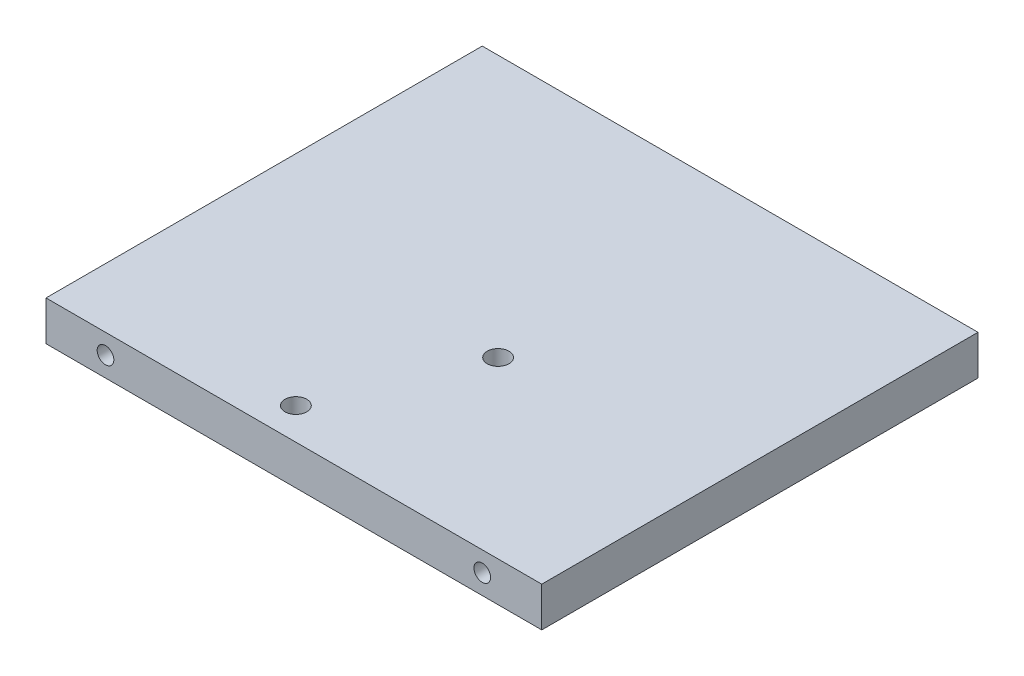
SolidWorks part; units mm, degrees
ref_plane "Front Plane" through (0, 0, 0) normal (0, 0, 1) x (1, 0, 0)
ref_plane "Top Plane" through (0, 0, 0) normal (0, 1, 0) x (1, 0, 0)
ref_plane "Right Plane" through (0, 0, 0) normal (1, 0, 0) x (0, 0, -1)
sketch "Sketch1" plane through (0, 0, 0) normal (0, 1, 0) x (1, 0, 0)
  line L1 (-62.5, -55) -> (62.5, -55)
  line L2 (-62.5, -55) -> (-62.5, 55)
  line L3 (-62.5, 55) -> (62.5, 55)
  line L4 (62.5, -55) -> (62.5, 55)
  line L5 (-62.5, -55) -> (62.5, 55) construction
  line L6 (-62.5, 55) -> (62.5, -55) construction
  circle A0 centre (7.5, -11) radius 2.75
  circle A1 centre (-7.5, -47) radius 2.75
  point P0 (0, 0)
  point P10 (0, 0)
  point P11 (0, 0)
  point P12 (0, 0)
  dimension "D3" = 5.5
  dimension "D4" = 5.5
  dimension "D1" = 125
  dimension "D2" = 110
  dimension "D5" = 8
  dimension "D6" = 11
  dimension "D7" = 7.5
  dimension "D8" = 7.5
extrude "Boss-Extrude1" add sketch "Sketch1" along normal blind 10
hole_wizard "M5 Tapped Hole3" positions "Sketch9" profile "Sketch10" tap size "M5" standard "DIN"
sketch "Sketch9" plane through (0, 0, -55) normal (0, 0, -1) x (-1, 0, 0)
  line L0 (-62.5, 10) -> (-62.5, 0) construction
  point P0 (-47.5, 5)
  point P2 (47.5, 5)
  point P7 (0, 0)
  point P8 (0, 0)
  dimension "D1" = 15
  dimension "D2" = 95
sketch "Sketch10" plane through (47.5, 5, -55) normal (1, 0, 0) x (0, 1, 0)
  line L0 (0, 0) -> (0, 17.2618)
  line L1 (0, 17.2618) -> (2.1, 16)
  line L2 (2.1, 16) -> (2.1, 0)
  line L5 (2.1, 0) -> (0, 0)
  line L10 (0, 17.2618) -> (-2.1, 16) construction
  line L11 (0, -6.35) -> (0, 107.95) construction
  dimension "Tap Drill Dia." = 4.2
  dimension "Tap Drill Depth" = 16
  dimension "Drill Angle" = 118
cosmetic thread "Hole Thread5" parameters "D1"=12, "D2"=5
cosmetic thread "Hole Thread6" parameters "D1"=12, "D2"=5
hole_wizard "M5 Tapped Hole4" positions "Sketch11" profile "Sketch12" tap size "M5" standard "DIN"
sketch "Sketch11" plane through (0, 0, 55) normal (0, 0, 1) x (1, 0, 0)
  line L0 (-62.5, 10) -> (-62.5, 0) construction
  point P0 (-47.5, 5)
  point P2 (47.5, 5)
  dimension "D1" = 15
  dimension "D2" = 95
sketch "Sketch12" plane through (-47.5, 5, 55) normal (1, 0, 0) x (0, -1, 0)
  line L0 (0, 0) -> (0, 17.2618)
  line L1 (0, 17.2618) -> (2.1, 16)
  line L2 (2.1, 16) -> (2.1, 0)
  line L5 (2.1, 0) -> (0, 0)
  line L10 (0, 17.2618) -> (-2.1, 16) construction
  line L11 (0, -6.35) -> (0, 107.95) construction
  dimension "Tap Drill Dia." = 4.2
  dimension "Tap Drill Depth" = 16
  dimension "Drill Angle" = 118
cosmetic thread "Hole Thread7" parameters "D1"=12, "D2"=5
cosmetic thread "Hole Thread8" parameters "D1"=12, "D2"=5
sketch "Sketch13" plane through (0, 0, 0) normal (0, -1, 0) x (-1, 0, 0)
  circle A0 centre (-7.5, -11) radius 5
  circle A1 centre (7.5, -47) radius 5
  dimension "D1" = 10
extrude "Cut-Extrude1" cut sketch "Sketch13" against normal blind 5.7
